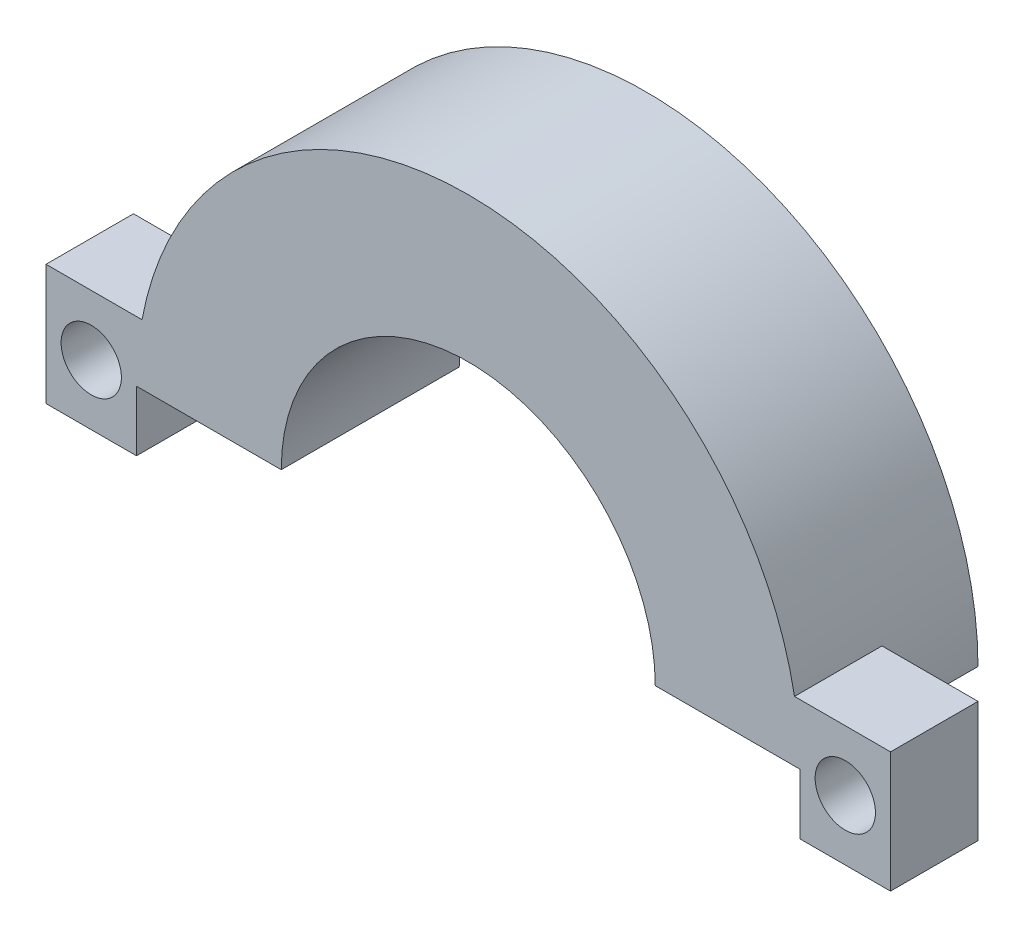
SolidWorks part; units mm, degrees
ref_plane "Plano frontal" through (0, 0, 0) normal (0, 0, 1) x (1, 0, 0)
ref_plane "Plano superior" through (0, 0, 0) normal (0, 1, 0) x (1, 0, 0)
ref_plane "Plano direito" through (0, 0, 0) normal (1, 0, 0) x (0, 0, -1)
sketch "Esboço1" plane through (0, 0, 0) normal (0, 0, 1) x (1, 0, 0)
  line L3 (-3.4368, 0) -> (18.5632, 0)
  arc A3 (-3.4368, 0) -> (18.5632, 0) centre (7.5632, 0) cw
  arc A4 (1.3632, 0) -> (13.7632, 0) centre (7.5632, 0) cw
  dimension "D2" = 6.2
  dimension "D1" = 22
extrude "Ressalto-extrusão1" add sketch "Esboço1" along normal blind 5.9 contours L3 A4 A3
sketch "Esboço2" plane through (0, 0, 5.9) normal (0, 0, 1) x (1, 0, 0)
  line L0 (18.5632, 0) -> (18.5632, -2)
  line L1 (15.5632, 2) -> (21.5632, 2)
  line L2 (15.5632, 2) -> (15.5632, -2)
  line L3 (15.5632, -2) -> (21.5632, -2)
  line L4 (21.5632, 2) -> (21.5632, -2)
  line L5 (-3.4368, 0) -> (-3.4368, -2)
  line L6 (-6.4368, 2) -> (-0.4368, 2)
  line L7 (-6.4368, 2) -> (-6.4368, -2)
  line L8 (-6.4368, -2) -> (-0.4368, -2)
  line L9 (-0.4368, 2) -> (-0.4368, -2)
  line L10 (-3.4368, 0) -> (-0.4368, 0)
  line L11 (18.5632, 0) -> (15.5632, 0)
  point P4 (21.5632, 0)
  point P12 (-6.4368, 0)
  line M5 (-3.4368, 0) -> (1.3632, 0)
  line M7 (13.7632, 0) -> (18.5632, 0)
  arc M8 (18.5632, 0) -> (-3.4368, 0) centre (7.5632, 0) ccw
  dimension "D1" = 4
  dimension "D2" = 3
  dimension "D3" = 6
  dimension "D4" = 6
  dimension "D5" = 4
  dimension "D6" = 3
extrude "Ressalto-extrusão2" add sketch "Esboço2" against normal blind 2.9 contours L7 L8 L5 L6 M8 | L9 L6 M8 M5 | L4 L1 L0 L3 M8 | L1 L2 M7 M8
sketch "Esboço3" plane through (0, 0, 5.9) normal (0, 0, 1) x (1, 0, 0)
  line L0 (21.5632, 2) -> (21.5632, -2) construction
  line L1 (-6.4368, 2) -> (-6.4368, -2) construction
  circle A0 centre (20.0632, 0) radius 1
  circle A1 centre (-4.9368, 0) radius 1
  point P9 (21.5632, 0)
  point P11 (-6.4368, 0)
  dimension "D1" = 2
  dimension "D3" = 2
  dimension "D2" = 1.5
  dimension "D4" = 1.5
  dimension "D5" = 25
extrude "Corte-extrusão1" cut sketch "Esboço3" against normal blind 6.5
